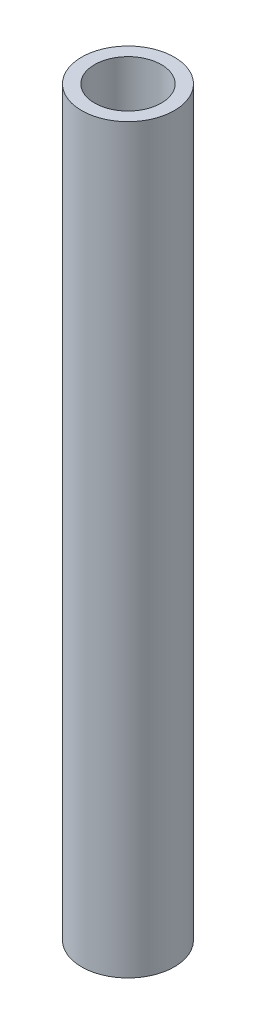
SolidWorks part; units mm, degrees
material "AISI 316 Stainless Steel Sheet (SS)"
ref_plane "Front Plane" through (0, 0, 0) normal (0, 0, 1) x (1, 0, 0)
ref_plane "Top Plane" through (0, 0, 0) normal (0, 1, 0) x (1, 0, 0)
ref_plane "Right Plane" through (0, 0, 0) normal (1, 0, 0) x (0, 0, -1)
sketch "Sketch1" plane through (0, 0, 0) normal (0, 1, 0) x (1, 0, 0)
  circle A0 centre (0, 0) radius 3.175
  circle A1 centre (0, 0) radius 2.286
  dimension "D1" = 6.35
  dimension "D2" = 4.572
extrude "Boss-Extrude1" add sketch "Sketch1" along normal blind 50.8
